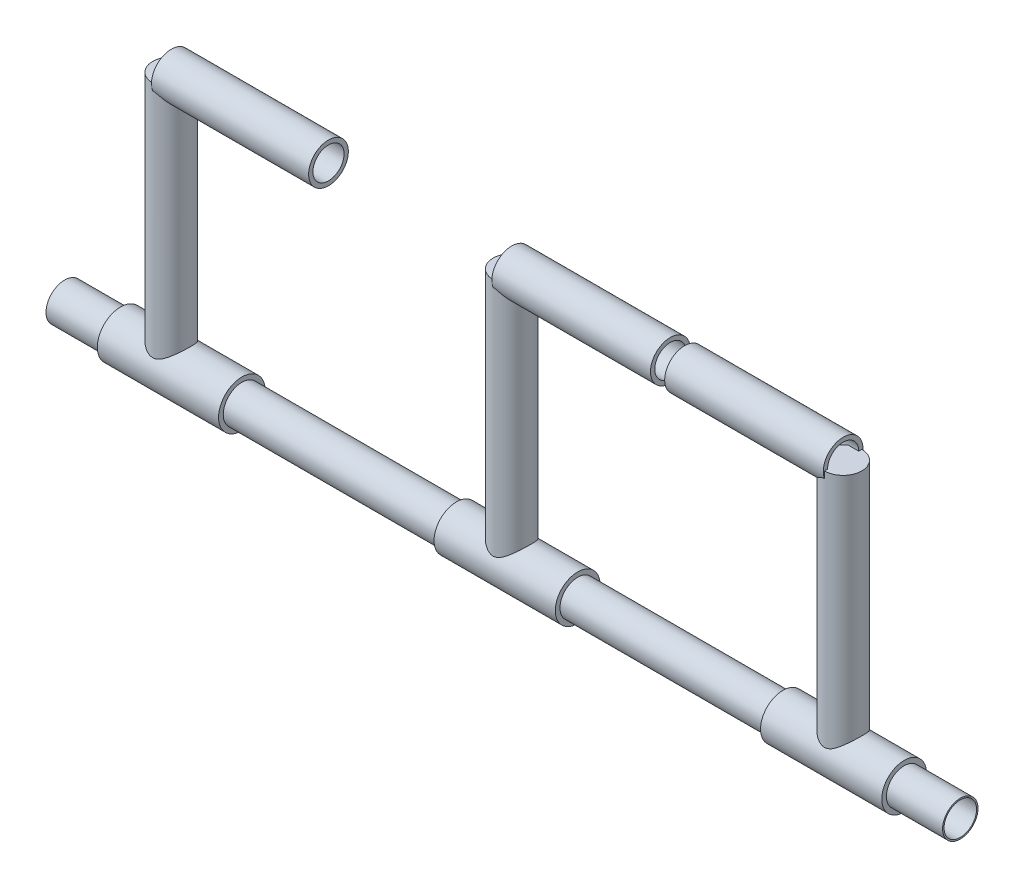
SolidWorks part; units mm, degrees
ref_plane "Front Plane" through (0, 0, 0) normal (0, 0, 1) x (1, 0, 0)
ref_plane "Top Plane" through (0, 0, 0) normal (0, 1, 0) x (1, 0, 0)
ref_plane "Right Plane" through (0, 0, 0) normal (1, 0, 0) x (0, 0, -1)
sketch "Sketch1" plane through (0, 0, 0) normal (0, 0, 1) x (1, 0, 0)
  line L0 (-63.8518, 0) -> (600, 0) construction
  line L1 (-57.1719, 0) -> (-57.1719, 10)
  line L2 (-57.1719, 10) -> (-27.1719, 10)
  line L3 (-27.1719, 10) -> (-27.1719, 12.5)
  line L4 (-27.1719, 12.5) -> (37.8281, 12.5)
  line L5 (37.8281, 12.5) -> (37.8281, 10)
  line L6 (37.8281, 10) -> (152.8281, 10)
  line L7 (152.8281, 10) -> (152.8281, 12)
  line L8 (152.8281, 12) -> (217.8281, 12)
  line L9 (217.8281, 12) -> (217.8281, 9.5)
  line L10 (217.8281, 9.5) -> (327.8281, 9.5)
  line L11 (327.8281, 9.5) -> (327.8281, 12)
  line L12 (327.8281, 12) -> (392.8281, 12)
  line L13 (392.8281, 12) -> (392.8281, 9.5)
  line L14 (392.8281, 9.5) -> (422.9189, 9.5)
  line L15 (422.9189, 9.5) -> (422.9189, 0)
  line L16 (-57.1719, 0) -> (422.9189, 0)
revolve "Revolve3" add sketch "Sketch1" angle 360 about L0
sketch "Sketch2" plane through (-57.1719, 0, 0) normal (-1, 0, 0) x (0, 0, 1)
  circle A0 centre (0, 0) radius 10
sketch "Sketch3" plane through (-57.1719, 0, 0) normal (-1, 0, 0) x (0, 0, 1)
  circle A0 centre (0, 0) radius 8.7217
extrude "Cut-Extrude2" cut sketch "Sketch3" against normal blind 500 and the other way blind 480
sketch "Sketch6" plane through (0, 0, 0) normal (0, 1, 0) x (1, 0, 0)
  circle A0 centre (0, 0) radius 10
extrude "Boss-Extrude1" add sketch "Sketch6" along normal blind 135.0694
sketch "Sketch7" plane through (0, 135.0694, 0) normal (0, 1, 0) x (1, 0, 0)
  line L0 (0, 0) -> (84.246, 0)
other "Structural Member1"
ref_plane "Plane1" through (0, 135.0694, 0) normal (1, 0, 0) x (0, 0, -1)
sketch "Sketch11" plane through (0, 135.0694, 0) normal (1, 0, 0) x (0, 0, -1)
  circle A0 centre (0, 0) radius 8.35
  circle A1 centre (0, 0) radius 10.65
  point P3 (0, 0)
  dimension "In_dia" = 16.7
  dimension "Out_dia" = 21.3
sketch "Sketch13" plane through (0, 0, 0) normal (0, 1, 0) x (1, 0, 0)
  circle A0 centre (182.477, 0) radius 10
  circle A1 centre (360.112, 0) radius 10
extrude "Boss-Extrude2" add sketch "Sketch13" along normal blind 135 separate body
sketch "Sketch14" plane through (0, 135, 0) normal (0, 1, 0) x (1, 0, 0)
  line L0 (360.112, 0) -> (275.112, 0)
sketch "Sketch15" plane through (0, 135, 0) normal (0, 1, 0) x (1, 0, 0)
  line L0 (182.477, 0) -> (267.477, 0)
other "Structural Member2"
ref_plane "Plane2" through (182.477, 135, 0) normal (1, 0, 0) x (0, 0, -1)
sketch "Sketch12" plane through (182.477, 135, 0) normal (1, 0, 0) x (0, 0, -1)
  circle A0 centre (0, 0) radius 8.35
  circle A1 centre (0, 0) radius 10.65
  point P3 (0, 0)
  dimension "In_dia" = 16.7
  dimension "Out_dia" = 21.3
